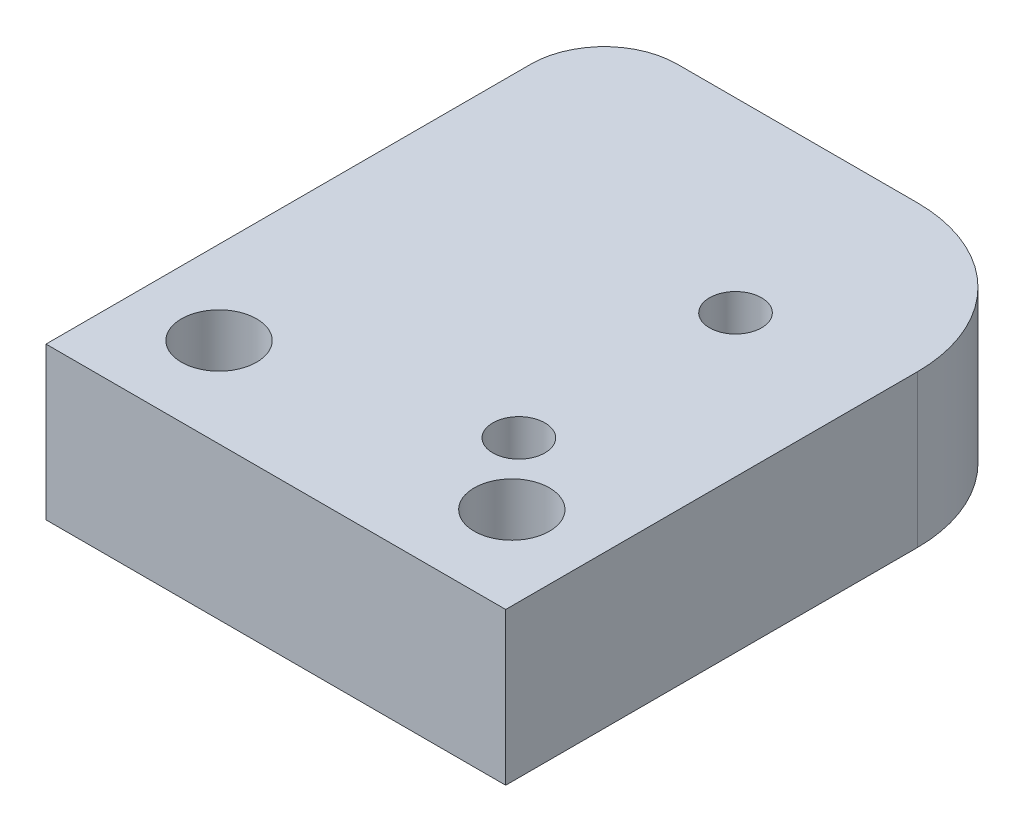
SolidWorks part; units mm, degrees
material "Acrylic (Blue)"
ref_plane "Front Plane" through (0, 0, 0) normal (0, 0, 1) x (1, 0, 0)
ref_plane "Top Plane" through (0, 0, 0) normal (0, 1, 0) x (1, 0, 0)
ref_plane "Right Plane" through (0, 0, 0) normal (1, 0, 0) x (0, 0, -1)
sketch "Sketch1" plane through (0, 0, 0) normal (0, 1, 0) x (1, 0, 0)
  line L1 (-9.9695, 24.2062) -> (9.9695, 24.2062)
  line L2 (-9.9695, 24.2062) -> (-9.9695, 0)
  line L3 (-9.9695, 0) -> (9.9695, 0)
  line L4 (9.9695, 24.2062) -> (9.9695, 0)
  dimension "D1" = 24.2062
  dimension "D2" = 19.939
extrude "Boss-Extrude1" add sketch "Sketch1" along normal blind 6.604
hole_wizard "#4-40 Tapped Hole1" positions "Sketch8" profile "Sketch9" tap size "#4-40" standard "ANSI Inch" end condition up to next
sketch "Sketch8" plane through (0, 6.604, 0) normal (0, 1, 0) x (1, 0, 0)
  line L0 (0, 0) -> (0, 11.43) construction
  line L1 (-9.9695, 0) -> (9.9695, 0) construction
  line L2 (0, 11.43) -> (3.81, 11.43) construction
  line L4 (3.81, 16.129) -> (3.81, 6.731) construction
  point P8 (3.81, 16.129)
  point P9 (3.81, 6.731)
  dimension "D1" = 9.398
  dimension "D2" = 3.81
  dimension "D3" = 11.43
sketch "Sketch9" plane through (3.81, 6.604, -16.129) normal (1, 0, 0) x (0, 0, 1)
  line L0 (0, 0) -> (0, 6.604)
  line L1 (0, 6.604) -> (1.1303, 6.604)
  line L2 (1.1303, 6.604) -> (1.1303, 0)
  line L5 (1.1303, 0) -> (0, 0)
  line L11 (0, -6.35) -> (0, 107.95) construction
  dimension "Thread Major Dia." = 2.2606
  dimension "Thru Tap Drill Depth" = 6.604
hole_wizard "CBORE for #4 Binding Head Machine Screw3" positions "Sketch11" profile "Sketch10" counterbore size "#4" standard "ANSI Inch" end condition through all
sketch "Sketch11" plane through (0, 0, 0) normal (0, -1, 0) x (-1, 0, 0)
  line L0 (0, 0) -> (0, 3.8862) construction
  line L2 (6.35, 3.8862) -> (-6.35, 3.8862) construction
  point P5 (6.35, 3.8862)
  point P6 (-6.35, 3.8862)
  dimension "D1" = 12.7
  dimension "D2" = 3.8862
sketch "Sketch10" plane through (-6.35, 0, -3.8862) normal (1, 0, 0) x (0, 0, -1)
  line L0 (0, 0) -> (0, 6.604)
  line L1 (0, 6.604) -> (1.6319, 6.604)
  line L3 (1.6319, 6.604) -> (1.632, 1.7272)
  line L4 (1.632, 1.7272) -> (2.4511, 1.7272)
  line L5 (2.4511, 1.7272) -> (2.4511, 0)
  line L7 (2.4511, 0) -> (0, 0)
  line L11 (0, -6.35) -> (0, 107.95) construction
  dimension "Thru Hole Dia." = 3.2639
  dimension "Thru Hole Depth" = 6.604
  dimension "C'Bore Dia." = 4.9022
  dimension "C'Bore Depth" = 1.7272
hole_wizard "CBORE for #4 Binding Head Machine Screw2" [suppressed] positions "Sketch3" profile "Sketch2" counterbore size "#4" standard "ANSI Inch"
sketch "Sketch3" plane through (0, 6.35, 0) normal (0, 1, 0) x (1, 0, 0)
  line L7 (0, 0) -> (0, 3.8862) construction
  line L9 (-6.35, 3.8862) -> (6.35, 3.8862) construction
  point P43 (-6.35, 3.8862)
  point P45 (6.35, 3.8862)
  dimension "D1" = 12.7
  dimension "D2" = 3.8862
sketch "Sketch2" plane through (-6.35, 6.35, -3.8862) normal (1, 0, 0) x (0, 0, 1)
  line L0 (0, 0) -> (0, 6.35)
  line L1 (0, 6.35) -> (1.632, 6.35)
  line L3 (1.632, 6.35) -> (1.6319, 1.7272)
  line L4 (1.6319, 1.7272) -> (2.4511, 1.7272)
  line L5 (2.4511, 1.7272) -> (2.4511, 0)
  line L7 (2.4511, 0) -> (0, 0)
  line L11 (0, -6.35) -> (0, 107.95) construction
  dimension "Thru Hole Dia." = 3.2639
  dimension "Thru Hole Depth" = 6.35
  dimension "C'Bore Dia." = 4.9022
  dimension "C'Bore Depth" = 1.7272
fillet "Fillet1" radius 6.35 1 edges at (9.9695, 3.302, -24.2062)
fillet "Fillet2" radius 3.175 1 edges at (-9.9695, 3.302, -24.2062)
other "Move Face1" [suppressed] parameters "D1"=0.0508
